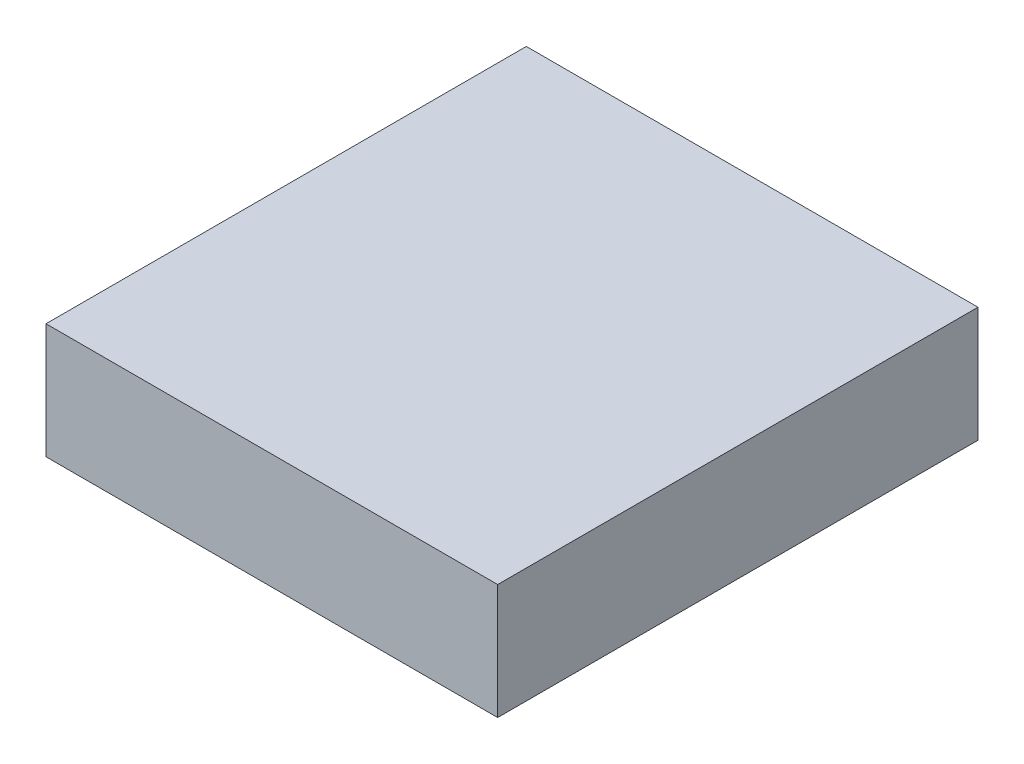
SolidWorks part; units mm, degrees
ref_plane "Front Plane" through (0, 0, 0) normal (0, 0, 1) x (1, 0, 0)
ref_plane "Top Plane" through (0, 0, 0) normal (0, 1, 0) x (1, 0, 0)
ref_plane "Right Plane" through (0, 0, 0) normal (1, 0, 0) x (0, 0, -1)
sketch "Sketch1" plane through (0, 0, 0) normal (0, 1, 0) x (1, 0, 0)
  line L1 (-45.085, 47.895) -> (45.085, 47.895)
  line L2 (-45.085, 47.895) -> (-45.085, -47.995)
  line L3 (-45.085, -47.995) -> (45.085, -47.995)
  line L4 (45.085, 47.895) -> (45.085, -47.995)
  dimension "D1" = 90.17
  dimension "D2" = 95.89
  dimension "D3" = 47.895
  dimension "D4" = 45.085
extrude "Boss-Extrude1" add sketch "Sketch1" along normal mid plane 23
